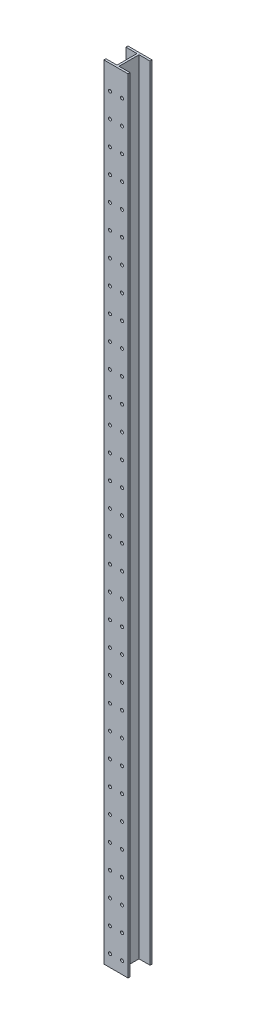
SolidWorks part; units mm, degrees
ref_plane "Front Plane" through (0, 0, 0) normal (0, 0, 1) x (1, 0, 0)
ref_plane "Top Plane" through (0, 0, 0) normal (0, 1, 0) x (1, 0, 0)
ref_plane "Right Plane" through (0, 0, 0) normal (1, 0, 0) x (0, 0, -1)
sketch "Sketch1" plane through (0, 0, 0) normal (0, 1, 0) x (1, 0, 0)
  line L0 (-4.318, 42.164) -> (4.318, 42.164) construction
  line L1 (-4.318, -42.164) -> (4.318, -42.164) construction
  line L2 (-4.318, -42.164) -> (-4.318, 42.164)
  line L3 (-4.318, 42.164) -> (4.318, 42.164) construction
  line L4 (4.318, -42.164) -> (4.318, 42.164)
  line L5 (-4.318, -42.164) -> (4.318, 42.164) construction
  line L6 (-4.318, 42.164) -> (4.318, -42.164) construction
  line L7 (-50.8, 42.164) -> (-4.318, 42.164)
  line L8 (-50.8, 42.164) -> (-50.8, 50.8)
  line L9 (-50.8, 50.8) -> (50.8, 50.8)
  line L10 (50.8, 42.164) -> (50.8, 50.8)
  line L11 (-50.8, -50.8) -> (50.8, -50.8)
  line L12 (-50.8, -50.8) -> (-50.8, -42.164)
  line L13 (-50.8, -42.164) -> (-4.318, -42.164)
  line L14 (50.8, -50.8) -> (50.8, -42.164)
  line L15 (4.318, 42.164) -> (50.8, 42.164)
  line L16 (-4.318, -42.164) -> (4.318, -42.164) construction
  line L17 (4.318, -42.164) -> (50.8, -42.164)
  point P0 (0, 0)
  point P14 (0, 0)
  point P15 (0, 0)
  point P16 (0, 0)
  point P17 (-31.3938, -25.4404)
  point P18 (44.9694, 101.6)
  point P19 (35.1069, -17.7605)
  point P20 (67.4541, 90.424)
  point P21 (0, 50.8)
  dimension "D1" = 8.636
  dimension "D2" = 101.6
  dimension "D3" = 8.636
  dimension "D4" = 101.6
extrude "Boss-Extrude1" add sketch "Sketch1" along normal blind 3302
sketch "Sketch2" plane through (0, 0, 50.8) normal (0, 0, 1) x (1, 0, 0)
  line L0 (0, 0) -> (0, -36.697) construction
  circle A0 centre (-25.4, 50.8) radius 6.35
  circle A1 centre (25.4, 50.8) radius 6.35
  point P5 (0, -36.697)
  dimension "D1" = 12.7
  dimension "D2" = 25.4
  dimension "D3" = 50.8
extrude "Cut-Extrude1" cut sketch "Sketch2" against normal up to next (8.636 mm away)
pattern_linear "LPattern1" count 32 spacing 101.6 along (0, 1, 0) of "Cut-Extrude1"
